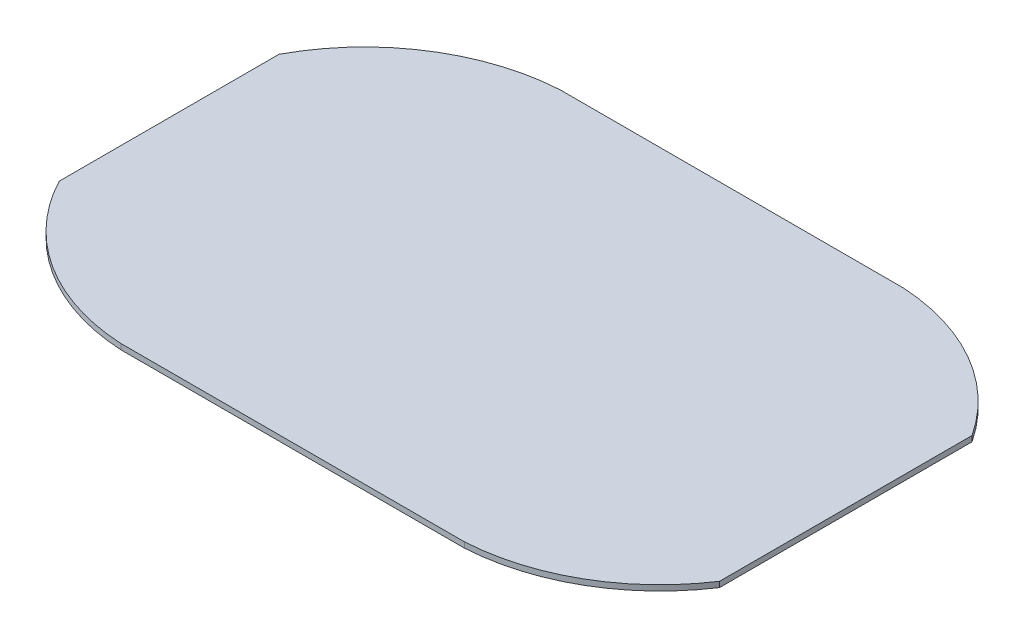
SolidWorks part; units mm, degrees
ref_plane "Front Plane" through (0, 0, 0) normal (0, 0, 1) x (1, 0, 0)
ref_plane "Top Plane" through (0, 0, 0) normal (0, 1, 0) x (1, 0, 0)
ref_plane "Right Plane" through (0, 0, 0) normal (1, 0, 0) x (0, 0, -1)
sketch "Sketch1" plane through (0, 0, 0) normal (0, 1, 0) x (1, 0, 0)
  line L1 (-125, -80) -> (125, -80)
  line L2 (-125, -80) -> (-125, 80)
  line L3 (-125, 80) -> (125, 80)
  line L4 (125, -80) -> (125, 80)
  line L5 (-125, -80) -> (125, 80) construction
  line L6 (-125, 80) -> (125, -80) construction
  point P0 (0, 0)
  dimension "D1" = 250
  dimension "D2" = 160
extrude "Boss-Extrude1" add sketch "Sketch1" along normal blind 2
sketch "Sketch5" plane through (0, 2, 0) normal (0, 1, 0) x (1, 0, 0)
  line L0 (-125, 40) -> (-125, 80)
  line L3 (125, 80) -> (-125, 80) construction
  line L4 (-125, 80) -> (-125, -80) construction
  line L6 (-125, 80) -> (-62.5, 80)
  line L7 (125, -80) -> (125, 80) construction
  line L8 (62.5, 80) -> (125, 80)
  line L9 (125, 80) -> (125, 40)
  line L10 (125, -40) -> (125, -80)
  line L11 (125, -80) -> (62.5, -80)
  line L12 (-62.5, -80) -> (-125, -80)
  line L13 (-125, -80) -> (125, -80) construction
  line L14 (-125, -80) -> (-125, -40)
  arc A0 (-62.5, 80) -> (-125, 40) centre (-58.1141, 4.3189) ccw
  arc A1 (-62.5, -80) -> (-125, -40) centre (-58.8595, -5.4836) cw
  arc A2 (125, -40) -> (62.5, -80) centre (58.1141, -4.3189) cw
  arc A3 (62.5, 80) -> (125, 40) centre (58.1141, 4.3189) cw
extrude "Cut-Extrude2" cut sketch "Sketch5" against normal blind 50
sketch "Sketch6" plane through (0, 2, 0) normal (0, 1, 0) x (1, 0, 0)
  line L1 (125, 76.782) -> (121.4479, 76.782)
  line L2 (125, 76.782) -> (125, -68.1458)
  line L3 (125, -68.1458) -> (121.4479, -68.1458)
  line L4 (121.4479, 76.782) -> (121.4479, -68.1458)
extrude "Cut-Extrude3" cut sketch "Sketch6" against normal blind 50
